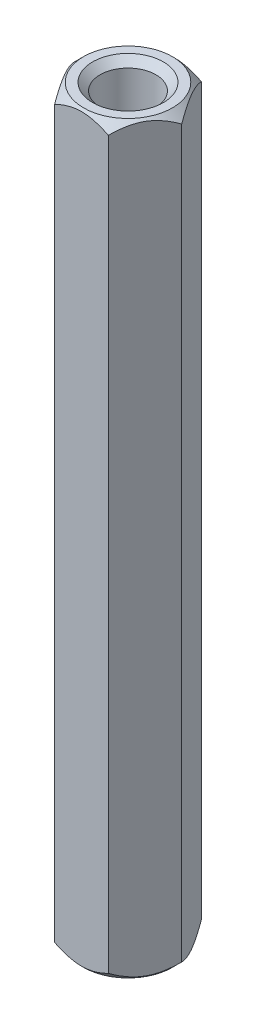
SolidWorks part; units mm, degrees
ref_plane "Front Plane" through (0, 0, 0) normal (0, 0, 1) x (1, 0, 0)
ref_plane "Top Plane" through (0, 0, 0) normal (0, 1, 0) x (1, 0, 0)
ref_plane "Right Plane" through (0, 0, 0) normal (1, 0, 0) x (0, 0, -1)
sketch "Sketch1" plane through (0, 0, 0) normal (0, 1, 0) x (1, 0, 0)
  line L1 (3.6662, 0) -> (1.8331, 3.175)
  line L2 (1.8331, 3.175) -> (-1.8331, 3.175)
  line L3 (-1.8331, 3.175) -> (-3.6662, 0)
  line L4 (-3.6662, 0) -> (-1.8331, -3.175)
  line L5 (-1.8331, -3.175) -> (1.8331, -3.175)
  line L6 (1.8331, -3.175) -> (3.6662, 0)
  circle A0 centre (0, 0) radius 3.175 construction
  circle A1 centre (0, 0) radius 1.905
  dimension "D1" = 3.81
  dimension "D2" = 6.35
extrude "Boss-Extrude1" add sketch "Sketch1" along normal blind 50.8
sketch "Sketch2" plane through (0, 0, 0) normal (0, 0, 1) x (1, 0, 0)
  line L0 (3.6662, 50.8) -> (3.0312, 50.8)
  line L1 (1.8331, 50.8) -> (3.6662, 50.8) construction
  line L2 (3.0312, 50.8) -> (3.9502, 49.8809)
  line L3 (3.9502, 49.8809) -> (3.6662, 50.8)
  line L4 (3.6662, 25.4) -> (14.6781, 25.4)
  line L5 (3.6662, 50.8) -> (3.6662, 0) construction
  line L6 (3.9502, 0.9191) -> (3.6662, 0)
  line L7 (3.0312, 0) -> (3.9502, 0.9191)
  line L8 (3.6662, 0) -> (3.0312, 0)
  line L9 (0, 49.8809) -> (0, 42.7055)
revolve "Cut-Revolve1" cut sketch "Sketch2" angle 360 about L9
chamfer "Chamfer1" distance 0.508 angle 45 2 edges at (0, 0, 1.905) (0, 50.8, 1.905)
